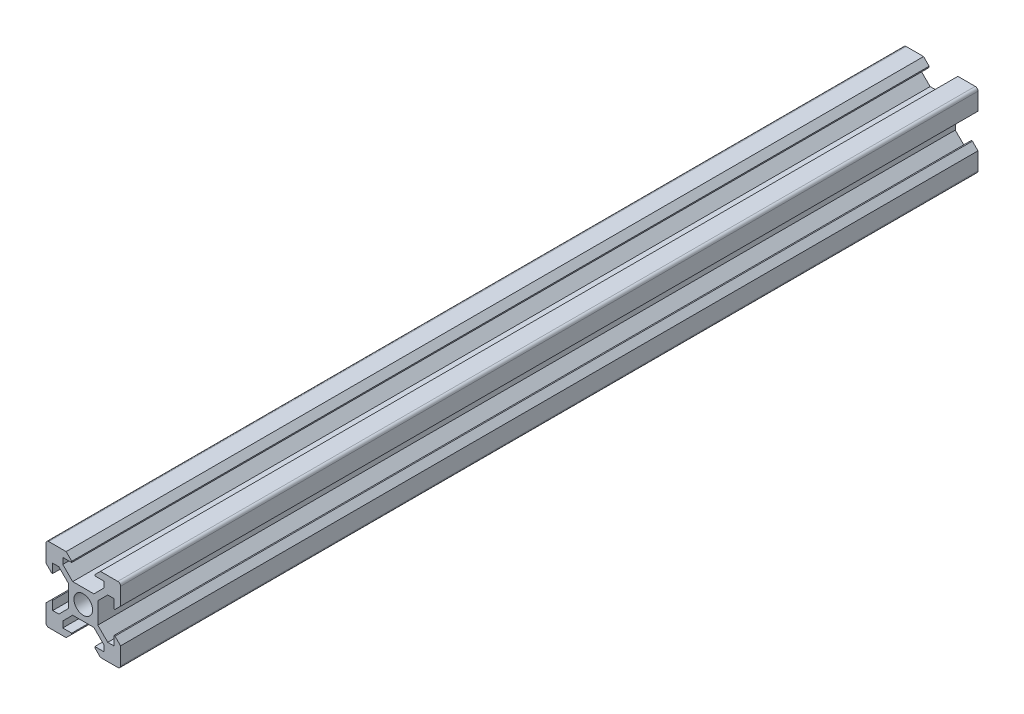
SolidWorks part; units mm, degrees
other "Markup1"
sketch "Sketch1" plane through (10, 10, 480) normal (0.5774, 0.5773, 0.5774) x (0.7071, 0, -0.7071)
ref_plane "Alzado" through (0, 0, 0) normal (0, 0, 1) x (1, 0, 0)
ref_plane "Planta" through (0, 0, 0) normal (0, 1, 0) x (1, 0, 0)
ref_plane "Vista lateral" through (0, 0, 0) normal (1, 0, 0) x (0, 0, -1)
sketch "Croquis1" plane through (0, 0, 0) normal (0, 0, 1) x (1, 0, 0)
  line L0 (-4.6, 10) -> (-3.1, 8.5)
  line L3 (-4.6, 10) -> (-9.25, 10)
  line L5 (-3.1, 8.5) -> (-3.1, 8.2)
  line L6 (-3.1, 8.2) -> (-5.5, 8.2)
  line L7 (-5.5, 8.2) -> (-5.5, 6.5607)
  line L8 (-5.5, 6.5607) -> (-2.84, 3.9007)
  line L9 (-2.84, 3.9007) -> (0, 3.9007)
  line L10 (0, 0) -> (-15.3499, 15.3499) construction
  line L11 (-3.9007, 2.84) -> (-3.9007, 0)
  line L12 (-6.5607, 5.5) -> (-3.9007, 2.84)
  line L13 (-8.2, 5.5) -> (-6.5607, 5.5)
  line L14 (-8.2, 3.1) -> (-8.2, 5.5)
  line L15 (-8.5, 3.1) -> (-8.2, 3.1)
  line L16 (-10, 4.6) -> (-10, 9.25)
  line L17 (-10, 4.6) -> (-8.5, 3.1)
  line L18 (10, 4.6) -> (8.5, 3.1)
  line L19 (10, 4.6) -> (10, 9.25)
  line L20 (8.5, 3.1) -> (8.2, 3.1)
  line L21 (8.2, 3.1) -> (8.2, 5.5)
  line L22 (8.2, 5.5) -> (6.5607, 5.5)
  line L23 (6.5607, 5.5) -> (3.9007, 2.84)
  line L24 (3.9007, 2.84) -> (3.9007, 0)
  line L25 (5.5, 6.5607) -> (2.84, 3.9007)
  line L26 (5.5, 8.2) -> (5.5, 6.5607)
  line L27 (3.1, 8.2) -> (5.5, 8.2)
  line L28 (3.1, 8.5) -> (3.1, 8.2)
  line L29 (4.6, 10) -> (9.25, 10)
  line L30 (4.6, 10) -> (3.1, 8.5)
  line L31 (2.84, 3.9007) -> (0, 3.9007)
  line L32 (4.6, -10) -> (3.1, -8.5)
  line L33 (4.6, -10) -> (9.25, -10)
  line L34 (3.1, -8.5) -> (3.1, -8.2)
  line L35 (3.1, -8.2) -> (5.5, -8.2)
  line L36 (5.5, -8.2) -> (5.5, -6.5607)
  line L37 (5.5, -6.5607) -> (2.84, -3.9007)
  line L38 (2.84, -3.9007) -> (0, -3.9007)
  line L39 (6.5607, -5.5) -> (3.9007, -2.84)
  line L40 (8.2, -5.5) -> (6.5607, -5.5)
  line L41 (8.2, -3.1) -> (8.2, -5.5)
  line L42 (8.5, -3.1) -> (8.2, -3.1)
  line L43 (10, -4.6) -> (10, -9.25)
  line L44 (10, -4.6) -> (8.5, -3.1)
  line L45 (3.9007, -2.84) -> (3.9007, 0)
  line L46 (-10, -4.6) -> (-8.5, -3.1)
  line L47 (-10, -4.6) -> (-10, -9.25)
  line L48 (-8.5, -3.1) -> (-8.2, -3.1)
  line L49 (-8.2, -3.1) -> (-8.2, -5.5)
  line L50 (-8.2, -5.5) -> (-6.5607, -5.5)
  line L51 (-6.5607, -5.5) -> (-3.9007, -2.84)
  line L52 (-3.9007, -2.84) -> (-3.9007, 0)
  line L53 (-5.5, -6.5607) -> (-2.84, -3.9007)
  line L54 (-5.5, -8.2) -> (-5.5, -6.5607)
  line L55 (-3.1, -8.2) -> (-5.5, -8.2)
  line L56 (-3.1, -8.5) -> (-3.1, -8.2)
  line L57 (-4.6, -10) -> (-9.25, -10)
  line L58 (-4.6, -10) -> (-3.1, -8.5)
  line L59 (-2.84, -3.9007) -> (0, -3.9007)
  circle A0 centre (0, 0) radius 2.5
  arc A1 (-9.25, 10) -> (-10, 9.25) centre (-9.25, 9.25) ccw
  arc A2 (10, 9.25) -> (9.25, 10) centre (9.25, 9.25) ccw
  arc A3 (9.25, -10) -> (10, -9.25) centre (9.25, -9.25) ccw
  arc A4 (-10, -9.25) -> (-9.25, -10) centre (-9.25, -9.25) ccw
  point P18 (-10, 10)
  point P37 (10, 10)
  point P55 (10, -10)
  point P73 (-10, -10)
  point P79 (0, 0)
  dimension "D1" = 5
  dimension "D5" = 0.75
  dimension "D2" = 10
  dimension "D3" = 10
  dimension "D4" = 4.6
  dimension "D6" = 5.5
  dimension "D7" = 135
  dimension "D8" = 0.75
  dimension "D9" = 225
  dimension "D10" = 2.84
  dimension "D11" = 1.8
  dimension "D12" = 3.1
  dimension "D13" = 4
extrude "Saliente-Extruir1" add sketch "Croquis1" along normal blind 230
